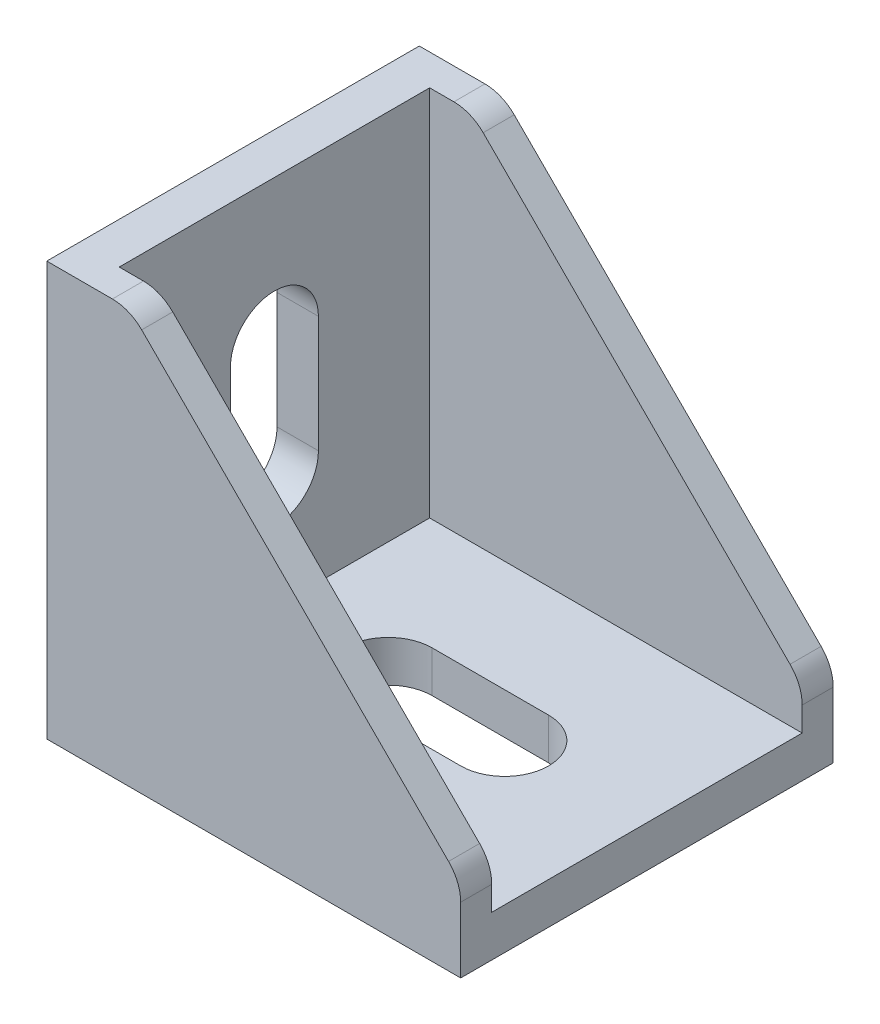
SolidWorks part; units mm, degrees
material "Алюминиевый сплав"
ref_plane "Спереди" through (0, 0, 0) normal (0, 0, 1) x (1, 0, 0)
ref_plane "Сверху" through (0, 0, 0) normal (0, 1, 0) x (1, 0, 0)
ref_plane "Справа" through (0, 0, 0) normal (1, 0, 0) x (0, 0, -1)
sketch "Эскиз1" plane through (0, 0, 0) normal (0, 0, 1) x (1, 0, 0)
  line L0 (0, 40) -> (0, 0)
  line L1 (0, 0) -> (40, 0)
  line L2 (40, 0) -> (40, 4)
  line L4 (4, 40) -> (0, 40)
  line L5 (4, 40) -> (4, 4)
  line L6 (4, 4) -> (40, 4)
  dimension "D1" = 40
  dimension "D2" = 4
extrude "Бобышка-Вытянуть1" add sketch "Эскиз1" along normal mid plane 36
sketch "Эскиз2" plane through (0, 0, 18) normal (0, 0, 1) x (1, 0, 0)
  line L1 (40, 4) -> (4, 4)
  line L2 (4, 4) -> (4, 40)
  line L3 (4, 40) -> (8, 40)
  line L4 (8, 40) -> (40, 8)
  line L5 (40, 8) -> (40, 4)
  line L6 (40, 0) -> (40, 4) construction
extrude "Бобышка-Вытянуть2" add sketch "Эскиз2" against normal blind 3
fillet "Скругление1" radius 4 2 edges at (40, 8, 16.5) (8, 40, 16.5)
mirror "Зеркальное отражение2" about plane through (0, 0, 0) normal (0, 0, 1) of "Скругление1", "Бобышка-Вытянуть2"
sketch "Эскиз3" plane through (0, 4, 0) normal (0, 1, 0) x (1, 0, 0)
  line L0 (15, 0) -> (26.25, 0) construction
  line L1 (15, 4.25) -> (26.25, 4.25)
  line L2 (15, -4.25) -> (26.25, -4.25)
  line L3 (0, -18) -> (0, 18) construction
  arc A0 (15, 4.25) -> (15, -4.25) centre (15, 0) ccw
  arc A1 (26.25, -4.25) -> (26.25, 4.25) centre (26.25, 0) ccw
  point P2 (20.625, 0)
  dimension "D2" = 4.25
  dimension "D3" = 15
  dimension "D1" = 11.25
extrude "Вырез-Вытянуть1" cut sketch "Эскиз3" against normal through all
sketch "Эскиз4" plane through (0, 0, 0) normal (0, -1, 0) x (1, 0, 0)
  line L0 (0, 18) -> (0, -18) construction
  line L1 (3, -3.9) -> (5.5, -3.9)
  line L2 (3, -3.9) -> (3, 3.9)
  line L3 (3, 3.9) -> (5.5, 3.9)
  line L4 (5.5, -3.9) -> (5.5, 3.9)
  line L5 (3, -3.9) -> (5.5, 3.9) construction
  line L6 (3, 3.9) -> (5.5, -3.9) construction
  line L7 (34.5, -3.9) -> (37, -3.9)
  line L8 (34.5, -3.9) -> (34.5, 3.9)
  line L9 (34.5, 3.9) -> (37, 3.9)
  line L10 (37, -3.9) -> (37, 3.9)
  line L11 (34.5, -3.9) -> (37, 3.9) construction
  line L12 (34.5, 3.9) -> (37, -3.9) construction
  line L13 (40, 18) -> (40, -18) construction
  point P0 (4.25, 0)
  point P5 (35.75, 0)
  dimension "D1" = 3
  dimension "D2" = 2.5
  dimension "D3" = 7.8
  dimension "D4" = 3
extrude "Бобышка-Вытянуть3" add sketch "Эскиз4" along normal blind 2.5
ref_plane "Плоскость1" through (0, 0, 0) normal (-0.7071, 0.7071, 0) x (0.7071, 0.7071, 0)
mirror "Зеркальное отражение3" about plane through (0, 0, 0) normal (-0.7071, 0.7071, 0) of "Бобышка-Вытянуть3", "Вырез-Вытянуть1"
